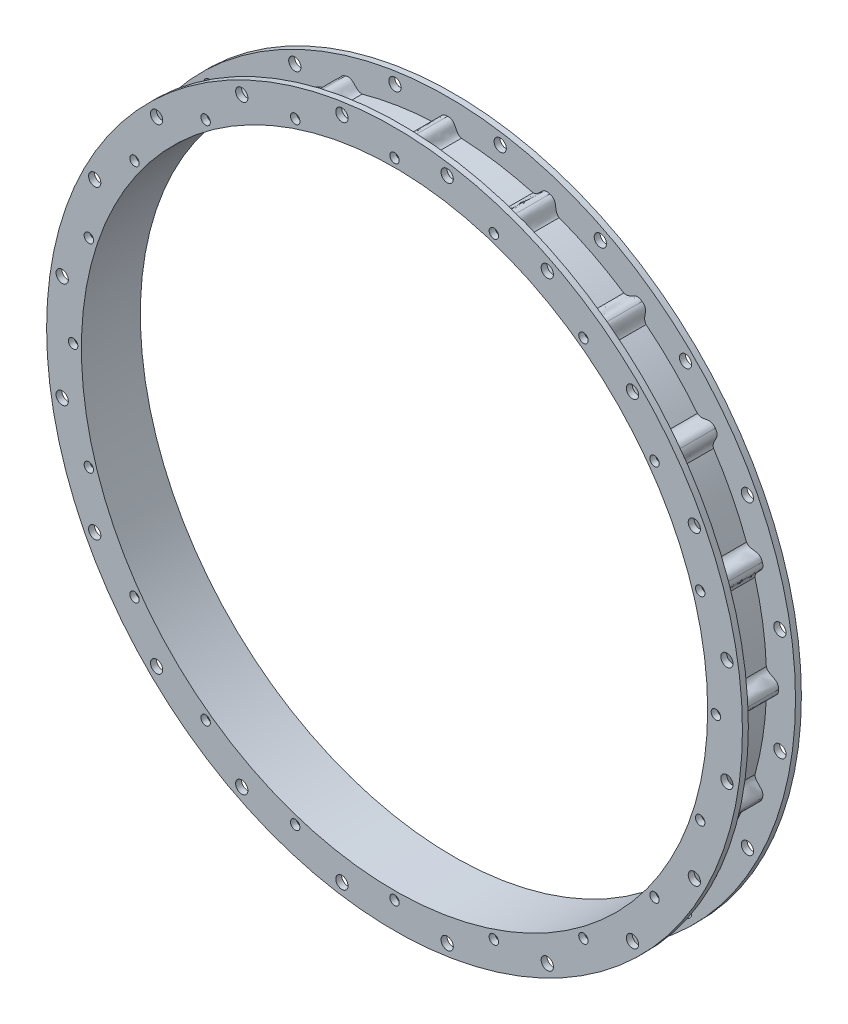
SolidWorks part; units mm, degrees
material "Maple"
ref_plane "Wasteboard" through (0, 0, 0) normal (0, 0, 1) x (1, 0, 0)
ref_plane "Left-Right" through (0, 0, 0) normal (0, 1, 0) x (1, 0, 0)
ref_plane "Front-Back" through (0, 0, 0) normal (1, 0, 0) x (0, 0, -1)
sketch "Sketch2" plane through (0, 0, 0) normal (0, 0, 1) x (1, 0, 0)
  circle A0 centre (0, 0) radius 192.0875 construction
  circle A1 centre (0, 0) radius 209.55 construction
  circle A2 centre (0, 0) radius 171.831 construction
  circle A3 centre (0, 0) radius 252.73 construction
  circle A4 centre (0, 0) radius 184.531 construction
  circle A5 centre (0, 0) radius 187.3885
  circle A6 centre (0, 0) radius 168.656
  dimension "D1" = 384.175
  dimension "D2" = 419.1
  dimension "D3" = 343.662
  dimension "D4" = 505.46
  dimension "D5" = 369.062
  dimension "D6" = 374.777
  dimension "D7" = 337.312
extrude "Boss-Extrude1" add sketch "Sketch2" along normal blind 3.175
sketch "Sketch3" plane through (0, 0, 3.175) normal (0, 0, 1) x (1, 0, 0)
  circle A0 centre (0, 0) radius 171.831
  circle A1 centre (0, 0) radius 168.656
  dimension "D1" = 343.662
extrude "Boss-Extrude2" add sketch "Sketch3" along normal blind 25.4
sketch "Sketch4" plane through (0, 0, 28.575) normal (0, 0, 1) x (1, 0, 0)
  circle A0 centre (0, 0) radius 187.3885
  circle A1 centre (0, 0) radius 168.656
extrude "Boss-Extrude3" add sketch "Sketch4" along normal blind 3.175
sketch "Sketch5" plane through (0, 0, 31.75) normal (0, 0, 1) x (1, 0, 0)
  line L0 (0, 0) -> (0, 196.8159) construction
  line L1 (-7.405, 171.6714) -> (7.405, 171.6714)
  line L2 (0, 178.2342) -> (22.1091, 178.2342) construction
  line L3 (50.9118, 162.6825) -> (45.3645, 143.4767) construction
  line L4 (46.0068, 165.5574) -> (60.092, 160.9809)
  line L5 (94.9151, 143.2376) -> (106.8967, 134.5325)
  line L6 (134.5325, 106.8967) -> (143.2376, 94.9151)
  line L7 (160.9809, 60.092) -> (165.5574, 46.0068)
  line L8 (171.6714, 7.405) -> (171.6714, -7.405)
  line L9 (165.5574, -46.0068) -> (160.9809, -60.092)
  line L10 (143.2376, -94.9151) -> (134.5325, -106.8967)
  line L11 (106.8967, -134.5325) -> (94.9151, -143.2376)
  line L12 (60.092, -160.9809) -> (46.0068, -165.5574)
  line L13 (7.405, -171.6714) -> (-7.405, -171.6714)
  line L14 (-46.0068, -165.5574) -> (-60.092, -160.9809)
  line L15 (-94.9151, -143.2376) -> (-106.8967, -134.5325)
  line L16 (-134.5325, -106.8967) -> (-143.2376, -94.9151)
  line L17 (-160.9809, -60.092) -> (-165.5574, -46.0068)
  line L18 (-171.6714, -7.405) -> (-171.6714, 7.405)
  line L19 (-165.5574, 46.0068) -> (-160.9809, 60.092)
  line L20 (-143.2376, 94.9151) -> (-134.5325, 106.8967)
  line L21 (-106.8967, 134.5325) -> (-94.9151, 143.2376)
  line L22 (-60.092, 160.9809) -> (-46.0068, 165.5574)
  circle A0 centre (0, 0) radius 171.831 construction
  circle A1 centre (0, 173.101) radius 1.27
  circle A3 centre (53.4912, 164.6288) radius 1.27
  circle A4 centre (101.7462, 140.0417) radius 1.27
  circle A5 centre (140.0417, 101.7462) radius 1.27
  circle A6 centre (164.6288, 53.4912) radius 1.27
  circle A7 centre (173.101, 0) radius 1.27
  circle A8 centre (164.6288, -53.4912) radius 1.27
  circle A9 centre (140.0417, -101.7462) radius 1.27
  circle A10 centre (101.7462, -140.0417) radius 1.27
  circle A11 centre (53.4912, -164.6288) radius 1.27
  circle A12 centre (0, -173.101) radius 1.27
  circle A13 centre (-53.4912, -164.6288) radius 1.27
  circle A14 centre (-101.7462, -140.0417) radius 1.27
  circle A15 centre (-140.0417, -101.7462) radius 1.27
  circle A16 centre (-164.6288, -53.4912) radius 1.27
  circle A17 centre (-173.101, 0) radius 1.27
  circle A18 centre (-164.6288, 53.4912) radius 1.27
  circle A19 centre (-140.0417, 101.7462) radius 1.27
  circle A20 centre (-101.7462, 140.0417) radius 1.27
  circle A21 centre (-53.4912, 164.6288) radius 1.27
  spline S0 degree 3 poles (0, 178.2342) (4.9619, 178.4345) (3.6283, 172.828) (7.405, 171.6714) knots 0 0 0 0 1 1 1 1
  spline S1 degree 3 poles (0, 178.2342) (-4.9619, 178.4345) (-3.6283, 172.828) (-7.405, 171.6714) knots 0 0 0 0 1 1 1 1
  spline S2 degree 3 poles (55.0774, 169.5108) (59.8584, 168.1679) (56.8575, 163.248) (60.092, 160.9809) knots 0 0 0 0 1 1 1 1
  spline S3 degree 3 poles (55.0774, 169.5108) (50.4202, 171.2346) (49.9561, 165.4904) (46.0068, 165.5574) knots 0 0 0 0 1 1 1 1
  spline S4 degree 3 poles (104.7634, 144.1945) (108.8954, 141.44) (104.5211, 137.6882) (106.8967, 134.5325) knots 0 0 0 0 1 1 1 1
  spline S5 degree 3 poles (104.7634, 144.1945) (100.8669, 147.2731) (98.6504, 141.9535) (94.9151, 143.2376) knots 0 0 0 0 1 1 1 1
  spline S6 degree 3 poles (144.1945, 104.7634) (147.2731, 100.8669) (141.9535, 98.6504) (143.2376, 94.9151) knots 0 0 0 0 1 1 1 1
  spline S7 degree 3 poles (144.1945, 104.7634) (141.44, 108.8954) (137.6882, 104.5211) (134.5325, 106.8967) knots 0 0 0 0 1 1 1 1
  spline S8 degree 3 poles (169.5108, 55.0774) (171.2346, 50.4202) (165.4904, 49.9561) (165.5574, 46.0068) knots 0 0 0 0 1 1 1 1
  spline S9 degree 3 poles (169.5108, 55.0774) (168.1679, 59.8584) (163.248, 56.8575) (160.9809, 60.092) knots 0 0 0 0 1 1 1 1
  spline S10 degree 3 poles (178.2342, 0) (178.4345, -4.9619) (172.828, -3.6283) (171.6714, -7.405) knots 0 0 0 0 1 1 1 1
  spline S11 degree 3 poles (178.2342, 0) (178.4345, 4.9619) (172.828, 3.6283) (171.6714, 7.405) knots 0 0 0 0 1 1 1 1
  spline S12 degree 3 poles (169.5108, -55.0774) (168.1679, -59.8584) (163.248, -56.8575) (160.9809, -60.092) knots 0 0 0 0 1 1 1 1
  spline S13 degree 3 poles (169.5108, -55.0774) (171.2346, -50.4202) (165.4904, -49.9561) (165.5574, -46.0068) knots 0 0 0 0 1 1 1 1
  spline S14 degree 3 poles (144.1945, -104.7634) (141.44, -108.8954) (137.6882, -104.5211) (134.5325, -106.8967) knots 0 0 0 0 1 1 1 1
  spline S15 degree 3 poles (144.1945, -104.7634) (147.2731, -100.8669) (141.9535, -98.6504) (143.2376, -94.9151) knots 0 0 0 0 1 1 1 1
  spline S16 degree 3 poles (104.7634, -144.1945) (100.8669, -147.2731) (98.6504, -141.9535) (94.9151, -143.2376) knots 0 0 0 0 1 1 1 1
  spline S17 degree 3 poles (104.7634, -144.1945) (108.8954, -141.44) (104.5211, -137.6882) (106.8967, -134.5325) knots 0 0 0 0 1 1 1 1
  spline S18 degree 3 poles (55.0774, -169.5108) (50.4202, -171.2346) (49.9561, -165.4904) (46.0068, -165.5574) knots 0 0 0 0 1 1 1 1
  spline S19 degree 3 poles (55.0774, -169.5108) (59.8584, -168.1679) (56.8575, -163.248) (60.092, -160.9809) knots 0 0 0 0 1 1 1 1
  spline S20 degree 3 poles (0, -178.2342) (-4.9619, -178.4345) (-3.6283, -172.828) (-7.405, -171.6714) knots 0 0 0 0 1 1 1 1
  spline S21 degree 3 poles (0, -178.2342) (4.9619, -178.4345) (3.6283, -172.828) (7.405, -171.6714) knots 0 0 0 0 1 1 1 1
  spline S22 degree 3 poles (-55.0774, -169.5108) (-59.8584, -168.1679) (-56.8575, -163.248) (-60.092, -160.9809) knots 0 0 0 0 1 1 1 1
  spline S23 degree 3 poles (-55.0774, -169.5108) (-50.4202, -171.2346) (-49.9561, -165.4904) (-46.0068, -165.5574) knots 0 0 0 0 1 1 1 1
  spline S24 degree 3 poles (-104.7634, -144.1945) (-108.8954, -141.44) (-104.5211, -137.6882) (-106.8967, -134.5325) knots 0 0 0 0 1 1 1 1
  spline S25 degree 3 poles (-104.7634, -144.1945) (-100.8669, -147.2731) (-98.6504, -141.9535) (-94.9151, -143.2376) knots 0 0 0 0 1 1 1 1
  spline S26 degree 3 poles (-144.1945, -104.7634) (-147.2731, -100.8669) (-141.9535, -98.6504) (-143.2376, -94.9151) knots 0 0 0 0 1 1 1 1
  spline S27 degree 3 poles (-144.1945, -104.7634) (-141.44, -108.8954) (-137.6882, -104.5211) (-134.5325, -106.8967) knots 0 0 0 0 1 1 1 1
  spline S28 degree 3 poles (-169.5108, -55.0774) (-171.2346, -50.4202) (-165.4904, -49.9561) (-165.5574, -46.0068) knots 0 0 0 0 1 1 1 1
  spline S29 degree 3 poles (-169.5108, -55.0774) (-168.1679, -59.8584) (-163.248, -56.8575) (-160.9809, -60.092) knots 0 0 0 0 1 1 1 1
  spline S30 degree 3 poles (-178.2342, 0) (-178.4345, 4.9619) (-172.828, 3.6283) (-171.6714, 7.405) knots 0 0 0 0 1 1 1 1
  spline S31 degree 3 poles (-178.2342, 0) (-178.4345, -4.9619) (-172.828, -3.6283) (-171.6714, -7.405) knots 0 0 0 0 1 1 1 1
  spline S32 degree 3 poles (-169.5108, 55.0774) (-168.1679, 59.8584) (-163.248, 56.8575) (-160.9809, 60.092) knots 0 0 0 0 1 1 1 1
  spline S33 degree 3 poles (-169.5108, 55.0774) (-171.2346, 50.4202) (-165.4904, 49.9561) (-165.5574, 46.0068) knots 0 0 0 0 1 1 1 1
  spline S34 degree 3 poles (-144.1945, 104.7634) (-141.44, 108.8954) (-137.6882, 104.5211) (-134.5325, 106.8967) knots 0 0 0 0 1 1 1 1
  spline S35 degree 3 poles (-144.1945, 104.7634) (-147.2731, 100.8669) (-141.9535, 98.6504) (-143.2376, 94.9151) knots 0 0 0 0 1 1 1 1
  spline S36 degree 3 poles (-104.7634, 144.1945) (-100.8669, 147.2731) (-98.6504, 141.9535) (-94.9151, 143.2376) knots 0 0 0 0 1 1 1 1
  spline S37 degree 3 poles (-104.7634, 144.1945) (-108.8954, 141.44) (-104.5211, 137.6882) (-106.8967, 134.5325) knots 0 0 0 0 1 1 1 1
  spline S38 degree 3 poles (-55.0774, 169.5108) (-50.4202, 171.2346) (-49.9561, 165.4904) (-46.0068, 165.5574) knots 0 0 0 0 1 1 1 1
  spline S39 degree 3 poles (-55.0774, 169.5108) (-59.8584, 168.1679) (-56.8575, 163.248) (-60.092, 160.9809) knots 0 0 0 0 1 1 1 1
  point P191 (0, 0)
  dimension "D1" = 2.54
  dimension "D2" = 20
extrude "Boss-Extrude4" add sketch "Sketch5" against normal blind 30.48
sketch "Sketch6" plane through (0, 0, 31.75) normal (0, 0, 1) x (1, 0, 0)
  line L0 (0, 0) -> (0, 196.8159) construction
  circle A1 centre (0, 173.101) radius 2.54
  circle A2 centre (53.4912, 164.6288) radius 2.54
  circle A22 centre (101.7462, 140.0417) radius 2.54
  circle A23 centre (140.0417, 101.7462) radius 2.54
  circle A24 centre (164.6288, 53.4912) radius 2.54
  circle A25 centre (173.101, 0) radius 2.54
  circle A26 centre (164.6288, -53.4912) radius 2.54
  circle A27 centre (140.0417, -101.7462) radius 2.54
  circle A28 centre (101.7462, -140.0417) radius 2.54
  circle A29 centre (53.4912, -164.6288) radius 2.54
  circle A30 centre (0, -173.101) radius 2.54
  circle A31 centre (-53.4912, -164.6288) radius 2.54
  circle A32 centre (-101.7462, -140.0417) radius 2.54
  circle A33 centre (-140.0417, -101.7462) radius 2.54
  circle A34 centre (-164.6288, -53.4912) radius 2.54
  circle A35 centre (-173.101, 0) radius 2.54
  circle A36 centre (-164.6288, 53.4912) radius 2.54
  circle A37 centre (-140.0417, 101.7462) radius 2.54
  circle A38 centre (-101.7462, 140.0417) radius 2.54
  circle A39 centre (-53.4912, 164.6288) radius 2.54
  point P45 (0, 0)
  point P191 (0, 0)
  dimension "D1" = 5.08
  dimension "D2" = 20
extrude "Cut-Extrude3" cut sketch "Sketch6" against normal blind 3.175
sketch "Sketch7" plane through (0, 0, 31.75) normal (0, 0, 1) x (1, 0, 0)
  line L0 (0, 0) -> (0, 203.459) construction
  circle A0 centre (28.3505, 178.9978) radius 3.302
  circle A2 centre (82.2762, 161.4762) radius 3.302
  circle A3 centre (128.1483, 128.1483) radius 3.302
  circle A4 centre (161.4762, 82.2762) radius 3.302
  circle A5 centre (178.9978, 28.3505) radius 3.302
  circle A6 centre (178.9978, -28.3505) radius 3.302
  circle A7 centre (161.4762, -82.2762) radius 3.302
  circle A8 centre (128.1483, -128.1483) radius 3.302
  circle A9 centre (82.2762, -161.4762) radius 3.302
  circle A10 centre (28.3505, -178.9978) radius 3.302
  circle A11 centre (-28.3505, -178.9978) radius 3.302
  circle A12 centre (-82.2762, -161.4762) radius 3.302
  circle A13 centre (-128.1483, -128.1483) radius 3.302
  circle A14 centre (-161.4762, -82.2762) radius 3.302
  circle A15 centre (-178.9978, -28.3505) radius 3.302
  circle A16 centre (-178.9978, 28.3505) radius 3.302
  circle A17 centre (-161.4762, 82.2762) radius 3.302
  circle A18 centre (-128.1483, 128.1483) radius 3.302
  circle A19 centre (-82.2762, 161.4762) radius 3.302
  circle A20 centre (-28.3505, 178.9978) radius 3.302
  point P45 (0, 0)
  dimension "D1" = 6.604
  dimension "D2" = 20
extrude "Cut-Extrude4" cut sketch "Sketch7" against normal through all
sketch "Sketch8" plane through (0, 0, 31.75) normal (0, 0, 1) x (1, 0, 0)
  line L0 (0, 0) -> (0, 217.7558)
